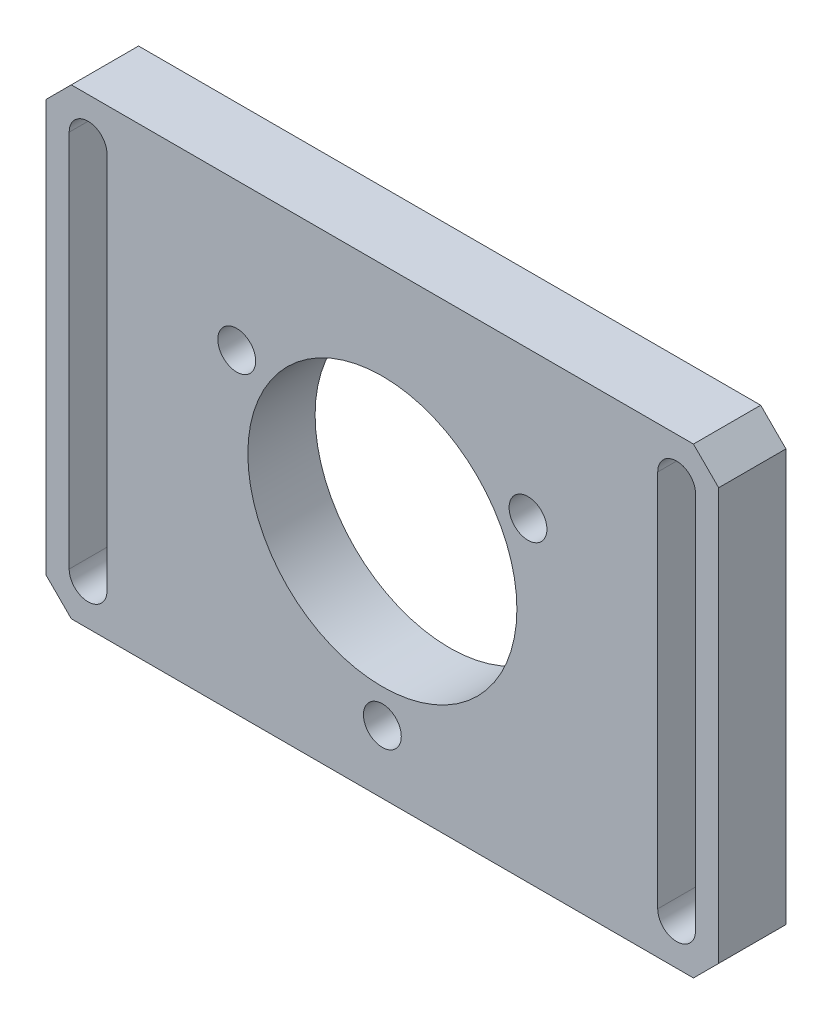
SolidWorks part; units mm, degrees
ref_plane "Front Plane" through (0, 0, 0) normal (0, 0, 1) x (1, 0, 0)
ref_plane "Top Plane" through (0, 0, 0) normal (0, 1, 0) x (1, 0, 0)
ref_plane "Right Plane" through (0, 0, 0) normal (1, 0, 0) x (0, 0, -1)
sketch "Sketch1" plane through (0, 0, 0) normal (0, 0, 1) x (1, 0, 0)
  line L1 (-29.6553, 16.2729) -> (50.3447, 16.2729)
  line L2 (-29.6553, 16.2729) -> (-29.6553, -38.7271)
  line L3 (-29.6553, -38.7271) -> (50.3447, -38.7271)
  line L4 (50.3447, 16.2729) -> (50.3447, -38.7271)
  line L6 (-26.9053, 11.2729) -> (-26.9053, -33.7271)
  line L8 (-22.4053, 11.2729) -> (-22.4053, -33.7271)
  line L10 (43.0947, 11.2729) -> (43.0947, -33.7271)
  line L12 (47.5947, 11.2729) -> (47.5947, -33.7271)
  circle A0 centre (10.3447, -11.2271) radius 16
  arc A1 (-22.4053, 11.2729) -> (-26.9053, 11.2729) centre (-24.6553, 11.2729) ccw
  arc A2 (-26.9053, -33.7271) -> (-22.4053, -33.7271) centre (-24.6553, -33.7271) ccw
  arc A3 (43.0947, -33.7271) -> (47.5947, -33.7271) centre (45.3447, -33.7271) ccw
  arc A4 (47.5947, 11.2729) -> (43.0947, 11.2729) centre (45.3447, 11.2729) ccw
  point P12 (10.3447, 16.2729)
  dimension "D3" = 32
  dimension "D4" = 4.5
  dimension "D5" = 4.5
  dimension "D1" = 80
  dimension "D2" = 55
  dimension "D9" = 45
  dimension "D11" = 45
extrude "Boss-Extrude1" add sketch "Sketch1" against normal blind 8
sketch "Sketch2" plane through (0, 0, 0) normal (0, 0, 1) x (1, 0, 0)
  circle A1 centre (10.3447, -31.2271) radius 2.25
  dimension "D2" = 4.5
extrude "Cut-Extrude1" cut sketch "Sketch2" against normal blind 8
pattern_circular "CirPattern1" count 3 over 360 about axis through (10.3447, -11.2271, 0) along (0, 0, 1) of "Cut-Extrude1"
chamfer "Chamfer1" distance 3 angle 45 4 edges at (50.3447, 16.2729, -4) (50.3447, -38.7271, -4) (-29.6553, -38.7271, -4) (-29.6553, 16.2729, -4)
